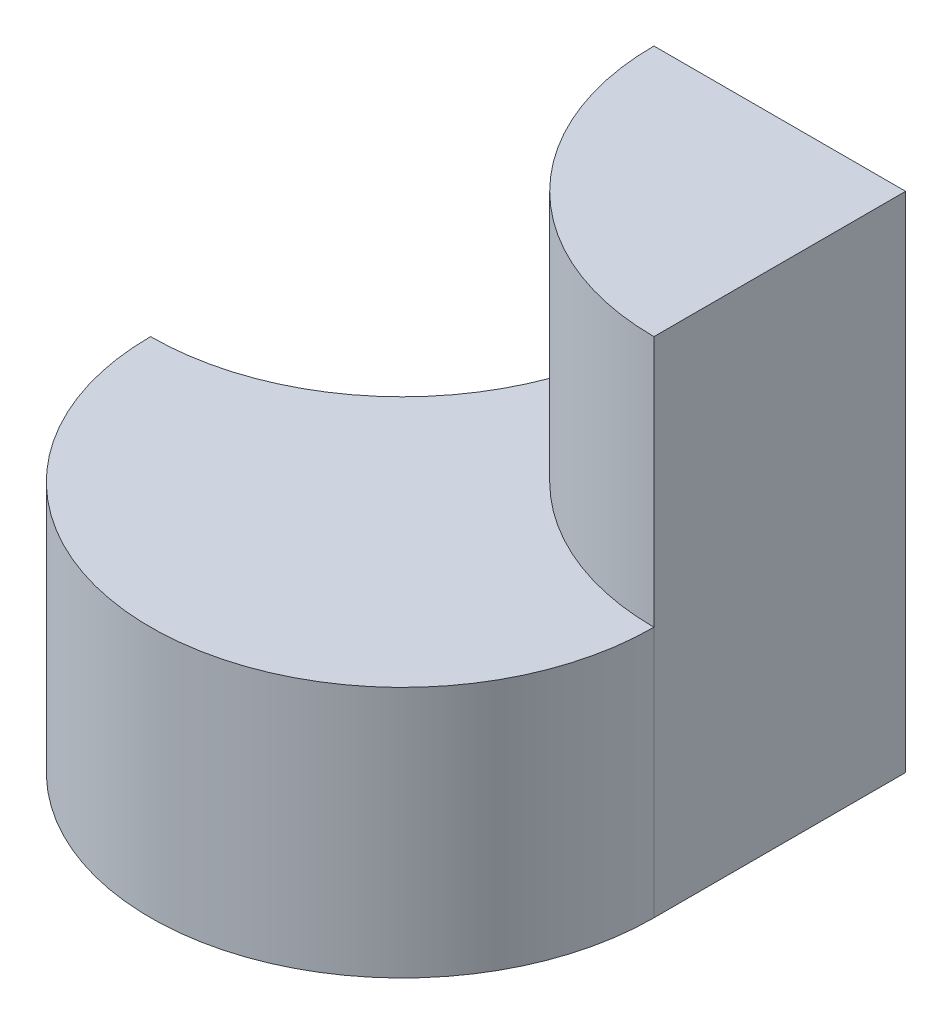
SolidWorks part; units mm, degrees
ref_plane "Front Plane" through (0, 0, 0) normal (0, 0, 1) x (1, 0, 0)
ref_plane "Top Plane" through (0, 0, 0) normal (0, 1, 0) x (1, 0, 0)
ref_plane "Right Plane" through (0, 0, 0) normal (1, 0, 0) x (0, 0, -1)
sketch "Sketch1" plane through (0, 0, 0) normal (0, 0, 1) x (1, 0, 0)
  line L0 (0, 0) -> (0, 40)
  line L1 (0, 40) -> (20, 40)
  line L2 (20, 40) -> (20, 20)
  line L3 (20, 20) -> (40, 20)
  line L4 (40, 20) -> (40, 0)
  line L5 (40, 0) -> (0, 0)
  dimension "D1" = 40
  dimension "D2" = 40
  dimension "D3" = 20
  dimension "D4" = 20
extrude "Boss-Extrude1" add sketch "Sketch1" along normal blind 40
sketch "Sketch2" plane through (0, 0, 0) normal (0, -1, 0) x (-1, 0, 0)
  line L0 (0, -40) -> (0, 0) construction
  line L1 (0, -20) -> (0, -40)
  line L2 (0, -40) -> (-40, -40)
  line L3 (-40, -40) -> (-40, -20)
  arc A0 (0, -20) -> (-40, -20) centre (-20, -20) cw
  line M2 (-40, 0) -> (-40, -40)
  line M3 (-40, -40) -> (0, -40)
  line M4 (0, -40) -> (0, 0)
  dimension "D1" = 20
  dimension "D2" = 20
  dimension "D3" = 20
  dimension "D4" = 20
extrude "Cut-Extrude1" cut sketch "Sketch2" against normal blind 40 contours A0 L2 M4 | A0 M3 M2
sketch "Sketch3" plane through (0, 20, 0) normal (0, 1, 0) x (1, 0, 0)
  line L0 (20, 0) -> (40, 0)
  line L1 (40, 0) -> (40, -20)
  line L3 (20, 0) -> (0, 0)
  line L4 (20, 0) -> (20, -20)
  line L5 (20, -20) -> (0, -20)
  line L6 (0, 0) -> (0, -20)
  arc A0 (20, 0) -> (40, -20) centre (40, 0) ccw
  arc A1 (20, -40) -> (40, -20) centre (20, -20) ccw construction
  line M1 (20, 0) -> (20, -40)
  dimension "D1" = 20
  dimension "D2" = 20
extrude "Cut-Extrude2" cut sketch "Sketch3" along normal blind 20 contours L3 L6 L5 M1
sketch "Sketch4" plane through (0, 20, 0) normal (0, 1, 0) x (1, 0, 0)
  line L0 (40, 0) -> (0, 0) construction
  line L1 (20, 0) -> (40, 0)
  line L2 (40, 0) -> (40, -20)
  arc A0 (20, 0) -> (40, -20) centre (40, 0) ccw
  arc A1 (20, -40) -> (40, -20) centre (20, -20) ccw construction
extrude "Boss-Extrude4" add sketch "Sketch4" along normal blind 20
sketch "Sketch5" plane through (0, 40, 0) normal (0, 1, 0) x (1, 0, 0)
  line L0 (0, -20) -> (20, -20)
  line L1 (20, -20) -> (20, -40)
  arc A0 (0, -20) -> (20, -40) centre (20, -20) ccw
extrude "Cut-Extrude3" cut sketch "Sketch5" against normal blind 20 contours A0 L0 L1
sketch "Sketch6" plane through (0, 0, 0) normal (-1, 0, 0) x (0, 0, 1)
  line L0 (0, 0) -> (20, 20)
  line L1 (20, 20) -> (0, 20)
  line L2 (0, 20) -> (0, 0)
  line L3 (0, 0) -> (0, 37.3863) construction
revolve "Cut-Revolve1" cut sketch "Sketch6" angle 360 about L3
